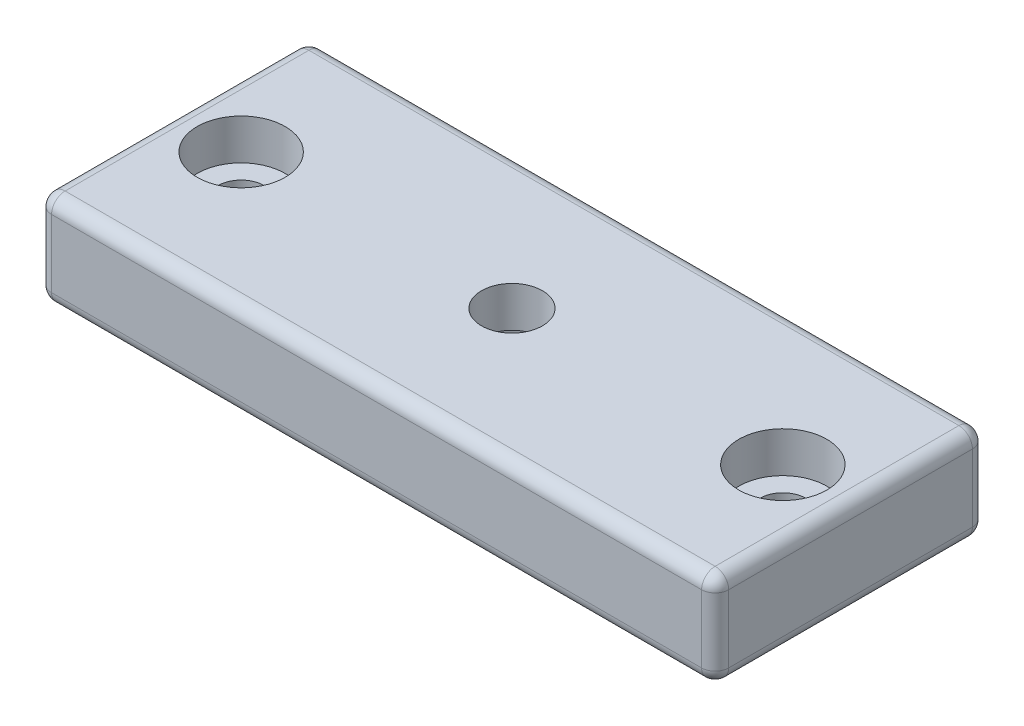
SolidWorks part; units mm, degrees
ref_plane "Front Plane" through (0, 0, 0) normal (0, 0, 1) x (1, 0, 0)
ref_plane "Top Plane" through (0, 0, 0) normal (0, 1, 0) x (1, 0, 0)
ref_plane "Right Plane" through (0, 0, 0) normal (1, 0, 0) x (0, 0, -1)
sketch "Sketch1" plane through (0, 0, 0) normal (0, 1, 0) x (1, 0, 0)
  line L1 (25, -10) -> (-25, -10)
  line L2 (25, -10) -> (25, 10)
  line L3 (25, 10) -> (-25, 10)
  line L4 (-25, -10) -> (-25, 10)
  line L5 (25, -10) -> (-25, 10) construction
  line L6 (25, 10) -> (-25, -10) construction
  point P0 (0, 0)
  dimension "D1" = 50
  dimension "D2" = 20
extrude "Extrude1" add sketch "Sketch1" along normal blind 7
hole_wizard "CBORE for M3 SHCS1" positions "Sketch6" profile "Sketch7" counterbore size "M3" standard "Ansi Metric" end condition through all
sketch "Sketch6" plane through (0, 7, 0) normal (0, 1, 0) x (-1, 0, 0)
  point P0 (20, 0)
  point P1 (-20, 0)
  dimension "D1" = 20
sketch "Sketch7" plane through (-20, 7, 0) normal (1, 0, 0) x (0, 0, 1)
  line L0 (0, 0) -> (0, 7)
  line L1 (0, 7) -> (1.7, 7)
  line L3 (1.7, 7) -> (1.7, 3)
  line L4 (1.7, 3) -> (3.25, 3)
  line L5 (3.25, 3) -> (3.25, 0)
  line L7 (3.25, 0) -> (0, 0)
  line L11 (0, -6.35) -> (0, 107.95) construction
  dimension "Thru Hole Dia." = 3.4
  dimension "Thru Hole Depth" = 7
  dimension "C'Bore Dia." = 6.5
  dimension "C'Bore Depth" = 3
fillet "Fillet1" radius 1 12 edges at (-25, 3.5, 10) (25, 3.5, 10) (25, 3.5, -10) (-25, 3.5, -10) (25, 7, 0) (25, 0, 0) (0, 0, 10) (0, 7, 10) (-25, 0, 0) (-25, 7, 0) (0, 7, -10) (0, 0, -10)
hole_wizard "CBORE for M4 SHCS1" positions "3DSketch4" profile "Sketch11" counterbore size "M4" standard "Ansi Metric" end condition through all
sketch3d "3DSketch4"
  point P0 (0, 0, 0)
  point P3 (0, 0, 0)
sketch "Sketch11" plane through (0, 0, 0) normal (1, 0, 0) x (0, 0, -1)
  line L0 (0, 0) -> (0, 7)
  line L1 (0, 7) -> (2.25, 7)
  line L3 (2.25, 7) -> (2.25, 4)
  line L4 (2.25, 4) -> (4, 4)
  line L5 (4, 4) -> (4, 0)
  line L7 (4, 0) -> (0, 0)
  line L11 (0, -6.35) -> (0, 107.95) construction
  dimension "Thru Hole Dia." = 4.5
  dimension "Thru Hole Depth" = 7
  dimension "C'Bore Dia." = 8
  dimension "C'Bore Depth" = 4
